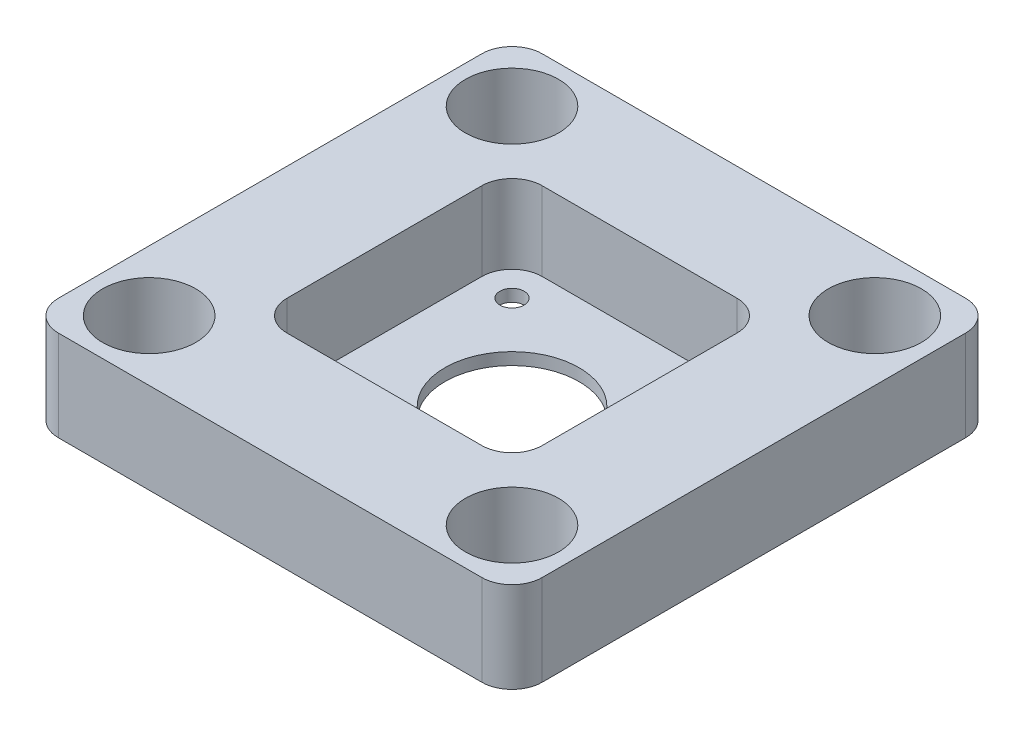
SolidWorks part; units mm, degrees
material "ABS"
ref_plane "Plano frontal" through (0, 0, 0) normal (0, 0, 1) x (1, 0, 0)
ref_plane "Plano superior" through (0, 0, 0) normal (0, 1, 0) x (1, 0, 0)
ref_plane "Plano direito" through (0, 0, 0) normal (1, 0, 0) x (0, 0, -1)
sketch "Esboço1" plane through (0, 0, 0) normal (0, 1, 0) x (1, 0, 0)
  line L1 (40, -40) -> (-40, -40)
  line L2 (40, -40) -> (40, 40)
  line L3 (40, 40) -> (-40, 40)
  line L4 (-40, -40) -> (-40, 40)
  line L5 (40, -40) -> (-40, 40) construction
  line L6 (40, 40) -> (-40, -40) construction
  point P0 (0, 0)
  dimension "D1" = 80
  dimension "D2" = 80
extrude "Ressalto-extrusão1" add sketch "Esboço1" along normal blind 15
sketch "Esboço2" plane through (0, 15, 0) normal (0, 1, 0) x (1, 0, 0)
  line L1 (21.1, -21.1) -> (-21.1, -21.1)
  line L2 (21.1, -21.1) -> (21.1, 21.1)
  line L3 (21.1, 21.1) -> (-21.1, 21.1)
  line L4 (-21.1, -21.1) -> (-21.1, 21.1)
  line L5 (21.1, -21.1) -> (-21.1, 21.1) construction
  line L6 (21.1, 21.1) -> (-21.1, -21.1) construction
  point P0 (0, 0)
  dimension "D1" = 42.2
  dimension "D2" = 42.2
extrude "Corte-extrusão1" cut sketch "Esboço2" against normal blind 13
fillet "Filete1" radius 5 4 edges at (21.1, 8.5, 21.1) (21.1, 8.5, -21.1) (-21.1, 8.5, 21.1) (-21.1, 8.5, -21.1)
sketch "Esboço3" plane through (0, 2, 0) normal (0, 1, 0) x (1, 0, 0)
  line L0 (56.5353, 0) -> (-65.9309, 0) construction
  line L1 (0, -55.1435) -> (0, 63.4292) construction
  circle A0 centre (0, 0) radius 11.1
  circle A1 centre (-15.5, 15.5) radius 2
  circle A2 centre (15.5, 15.5) radius 2
  circle A3 centre (15.5, -15.5) radius 2
  circle A4 centre (-15.5, -15.5) radius 2
  dimension "D1" = 22.2
  dimension "D2" = 4
  dimension "D3" = 15.5
  dimension "D4" = 15.5
extrude "Corte-extrusão2" cut sketch "Esboço3" against normal through all
sketch "Esboço4" plane through (0, 15, 0) normal (0, 1, 0) x (1, 0, 0)
  line L0 (40, 40) -> (-40, 40) construction
  line L1 (-40, 40) -> (-40, -40) construction
  line L2 (63.987, 0) -> (-58.3172, 0) construction
  line L3 (0, -45.4389) -> (0, 42.847) construction
  circle A0 centre (-30, 30) radius 7.7
  circle A1 centre (30, 30) radius 7.7
  circle A2 centre (30, -30) radius 7.7
  circle A3 centre (-30, -30) radius 7.7
  dimension "D1" = 15.4
  dimension "D2" = 10
  dimension "D3" = 10
extrude "Corte-extrusão3" cut sketch "Esboço4" against normal through all
fillet "Filete2" radius 5 4 edges at (-40, 7.5, -40) (40, 7.5, -40) (40, 7.5, 40) (-40, 7.5, 40)
